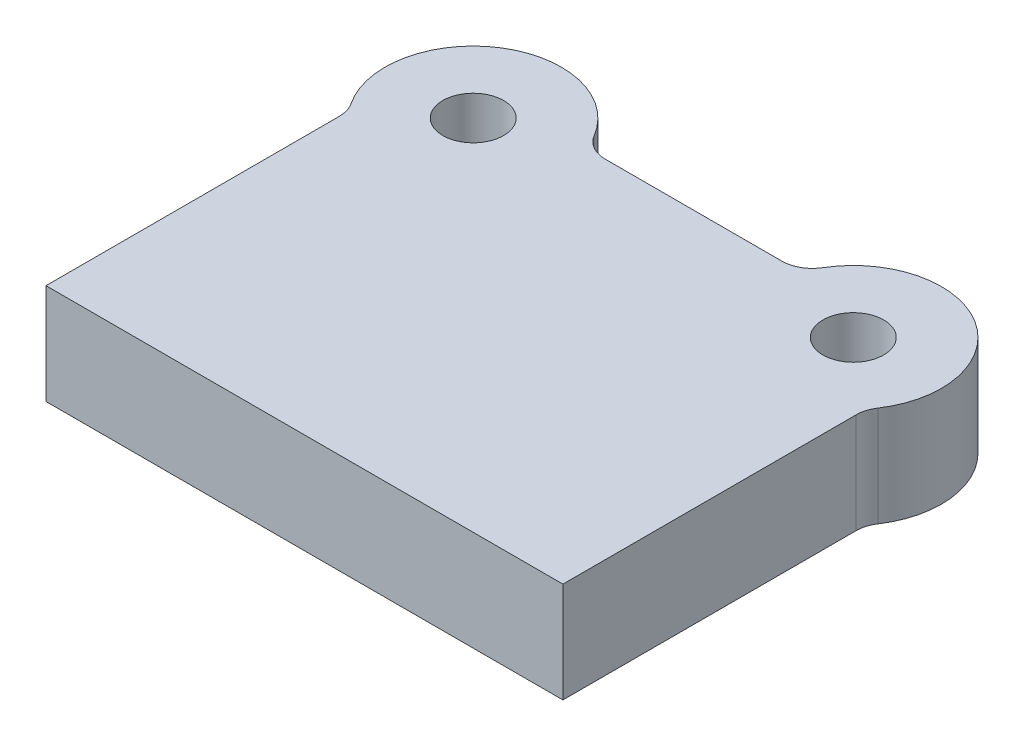
SolidWorks part; units mm, degrees
ref_plane "Front Plane" through (0, 0, 0) normal (0, 0, 1) x (1, 0, 0)
ref_plane "Top Plane" through (0, 0, 0) normal (0, 1, 0) x (1, 0, 0)
ref_plane "Right Plane" through (0, 0, 0) normal (1, 0, 0) x (0, 0, -1)
sketch "Sketch1" plane through (0, 0, 0) normal (0, 1, 0) x (1, 0, 0)
  line L0 (85, 0) -> (-85, 0)
  line L1 (-85, 0) -> (-85, 99.7038)
  line L2 (0, 0) -> (0, 128) construction
  line L3 (35.2787, 128) -> (-35.2787, 128)
  line L4 (85, 0) -> (85, 99.7038)
  arc A0 (-35.2787, 128) -> (-85, 99.7038) centre (-62.5, 118) ccw
  circle A1 centre (-62.5, 118) radius 10
  circle A2 centre (62.5, 118) radius 10
  arc A3 (35.2787, 128) -> (85, 99.7038) centre (62.5, 118) cw
  point P9 (-80.3731, 118)
  point P10 (-98.2907, 86.9659)
  point P11 (-45.743, 127.2148)
  dimension "D3" = 58
  dimension "D4" = 20
  dimension "D1" = 118
  dimension "D2" = 128
  dimension "D5" = 170
  dimension "D6" = 125
extrude "Boss-Extrude1" add sketch "Sketch1" along normal blind 33
fillet "Fillet1" radius 10 4 edges at (-85, 16.5, -99.7038) (-35.2787, 16.5, -128) (35.2787, 16.5, -128) (85, 16.5, -99.7038)
